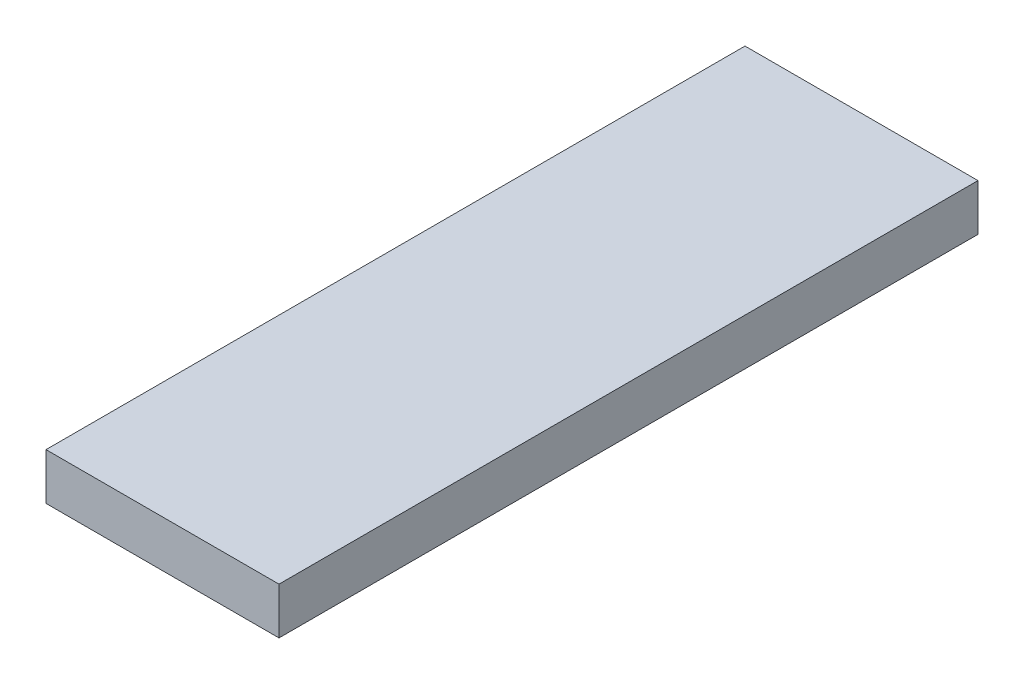
SolidWorks part; units mm, degrees
ref_plane "前视基准面" through (0, 0, 0) normal (0, 0, 1) x (1, 0, 0)
ref_plane "上视基准面" through (0, 0, 0) normal (0, 1, 0) x (1, 0, 0)
ref_plane "右视基准面" through (0, 0, 0) normal (1, 0, 0) x (0, 0, -1)
sketch "草图1" plane through (0, 0, 0) normal (0, 1, 0) x (1, 0, 0)
  line L0 (-17.8484, 18.716) -> (-7.8484, 18.716)
  line L1 (-7.8484, 18.716) -> (-7.8484, -11.284)
  line L2 (-7.8484, -11.284) -> (-17.8484, -11.284)
  line L3 (-17.8484, -11.284) -> (-17.8484, 18.716)
extrude "凸台-拉伸1" add sketch "草图1" along normal blind 2
